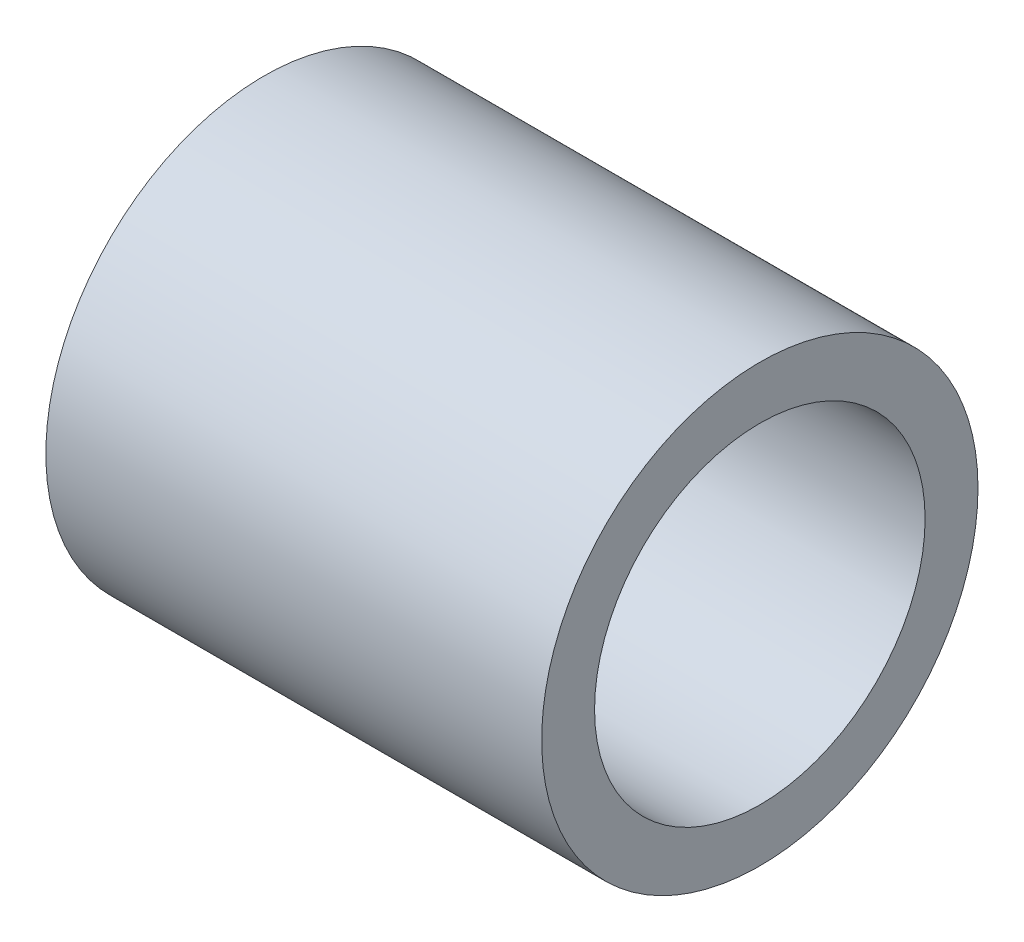
SolidWorks part; units mm, degrees
ref_plane "Front Plane" through (0, 0, 0) normal (0, 0, 1) x (1, 0, 0)
ref_plane "Top Plane" through (0, 0, 0) normal (0, 1, 0) x (1, 0, 0)
ref_plane "Right Plane" through (0, 0, 0) normal (1, 0, 0) x (0, 0, -1)
sketch "Sketch1" plane through (0, 0, 0) normal (1, 0, 0) x (0, 0, -1)
  circle A0 centre (0, 0) radius 3.175
  circle A1 centre (0, 0) radius 4.191
  dimension "D1" = 6.35
  dimension "D2" = 1.016
extrude "Boss-Extrude1" add sketch "Sketch1" along normal blind 9.525
